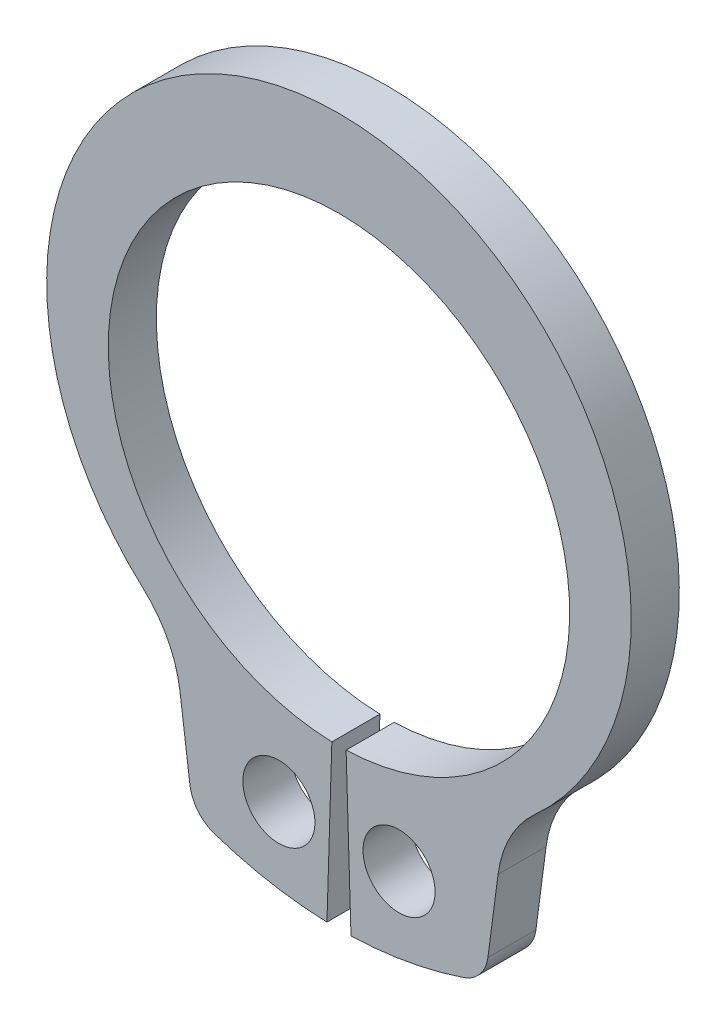
SolidWorks part; units mm, degrees
ref_plane "Plane1" through (0, 0, 0) normal (0, 0, 1) x (1, 0, 0)
ref_plane "Plane2" through (0, 0, 0) normal (0, 1, 0) x (1, 0, 0)
ref_plane "Plane3" through (0, 0, 0) normal (1, 0, 0) x (0, 0, -1)
sketch "Clipboard" plane through (0, 0, 0) normal (0, 0, 1) x (1, 0, 0)
  line L0 (0, 0) -> (1.8, 0)
  line L1 (0, 0) -> (0, 0.9)
  line L2 (0, 0) -> (0, -3.3)
  circle A0 centre (0, 0) radius 0.75
  circle A1 centre (0, 0) radius 5
  dimension "HoleDia" = 1.5
  dimension "ShaftDia" = 10
  dimension "LargeSection" = 1.8
  dimension "SmallSection" = 0.9
  dimension "LugSection" = 3.3
sketch "BodySke" plane through (0, 0, 0) normal (0, 0, 1) x (1, 0, 0)
  line L0 (-1.5431, 0) -> (1.5431, 0) construction
  line L1 (0, 0) -> (0, 6.6) construction
  line L2 (0.1481, -4.7977) -> (0.25, -8.0961)
  line L3 (-0.1481, -4.7977) -> (-0.25, -8.0961)
  line L4 (0, 0) -> (5.6861, -5.7688) construction
  line L5 (0, 0) -> (-5.6861, -5.7688) construction
  line L7 (3.3097, -5.4559) -> (3.0984, -7.0605)
  line L8 (-3.3097, -5.4559) -> (-3.0984, -7.0605)
  circle A0 centre (0, 0) radius 4.8 construction
  arc A1 (0.1481, -4.7977) -> (-0.1481, -4.7977) centre (0, 0) ccw
  arc A2 (4.0013, -4.0595) -> (-4.0013, -4.0595) centre (0, 0.5193) ccw construction
  arc A3 (0.25, -8.0961) -> (2.5951, -7.673) centre (0, 0) ccw
  arc A4 (4.0784, -3.991) -> (3.3097, -5.4559) centre (5.6861, -5.7688) ccw
  arc A5 (-3.3097, -5.4559) -> (-4.0784, -3.991) centre (-5.6861, -5.7688) ccw
  arc A6 (-2.5951, -7.673) -> (-0.25, -8.0961) centre (0, 0) ccw
  arc A7 (4.0784, -3.991) -> (-4.0784, -3.991) centre (0, 0.5193) ccw
  arc A8 (-3.2816, -5.6686) -> (3.2816, -5.6686) centre (0, 0) ccw construction
  circle A9 centre (1.25, -6.4296) radius 0.75
  circle A10 centre (-1.25, -6.4296) radius 0.75
  arc A11 (3.0984, -7.0605) -> (2.5951, -7.673) centre (2.3548, -6.9626) cw
  arc A12 (-3.0984, -7.0605) -> (-2.5951, -7.673) centre (-2.3548, -6.9626) ccw
  point P28 (3.0395, -7.5081)
  point P31 (-3.0395, -7.5081)
  dimension "GrooveDia" = 9.6
  dimension "D3" = 0.75
  dimension "LugRad" = 8.1
  dimension "HoleOffsetRad" = 6.55
  dimension "HoleDia" = 1.5
  dimension "D2" = 15
  dimension "LargeRad" = 6.6
  dimension "SmallRad" = 5.7
  dimension "Gap" = 0.5
  dimension "SmallAngle" = 89.172
  dimension "HoleSpacing" = 2.5
extrude "Body" add sketch "BodySke" against normal blind 1
sketch "NotSke" plane through (0, 0, 0) normal (0, 0, 1) x (1, 0, 0)
  line L0 (1.25, -5.6796) -> (1.25, -7.1796)
  line L1 (1.25, -7.1796) -> (-1.25, -7.1796)
  line L2 (-1.25, -7.1796) -> (-1.25, -5.6796)
  line L3 (-1.25, -5.6796) -> (1.25, -5.6796)
  circle A0 centre (1.25, -6.4296) radius 0.75 construction
  circle A1 centre (-1.25, -6.4296) radius 0.75 construction
extrude "Notch" [suppressed] cut sketch "NotSke" against normal through all
sketch "UnlSke" plane through (0, 0, 0) normal (0, 0, 1) x (1, 0, 0)
  line L0 (-2.4461, -7.7218) -> (-1.4495, -4.5759)
  line L1 (2.4461, -7.7218) -> (1.4495, -4.5759)
  arc A0 (1.4495, -4.5759) -> (-1.4495, -4.5759) centre (0, 0) ccw
  arc A1 (2.4461, -7.7218) -> (-2.4461, -7.7218) centre (0, 0) ccw
  arc A2 (0.25, -8.0961) -> (2.5951, -7.673) centre (0, 0) ccw construction
  arc A3 (0.1481, -4.7977) -> (-0.1481, -4.7977) centre (0, 0) ccw construction
  circle A4 centre (-1.25, -6.4296) radius 0.75 construction
  circle A5 centre (1.25, -6.4296) radius 0.75 construction
extrude "Unlug" [suppressed] add sketch "UnlSke" against normal through all
equation "' \"ShaftDia@Clipboard\" = 3"
equation "' \"Thickness@Body\" = 0.4"
equation "' \"GrooveDia@BodySke\" = 2.8"
equation "' \"LugSection@Clipboard\" = 1.9"
equation "' \"LargeSection@Clipboard\" = 0.8"
equation "' \"HoleDia@Clipboard\" = 1.0"
equation "' \"ShaftDia@Clipboard\" = 10"
equation "' \"Thickness@Body\" = 1.0"
equation "' \"GrooveDia@BodySke\" = 9.6"
equation "' \"LugSection@Clipboard\" = 3.3"
equation "' \"LargeSection@Clipboard\" = 1.8"
equation "' \"HoleDia@Clipboard\" = 1.5"
equation "\"SmallSection@Clipboard\" = \"LargeSection@Clipboard\" * 0.5"
equation "\"Gap@BodySke\" =  \"Thickness@Body\" / 2"
equation "\"LargeRad@BodySke\" =  \"GrooveDia@BodySke\" / 2 +  \"LargeSection@Clipboard\""
equation "\"SmallRad@BodySke\" =  \"GrooveDia@BodySke\" / 2 +  \"SmallSection@Clipboard\""
equation "\"LugRad@BodySke\" = \"GrooveDia@BodySke\" / 2 + \"LugSection@Clipboard\""
equation "\"HoleOffsetRad@BodySke\" = (  \"ShaftDia@Clipboard\" / 2 + \"LugRad@BodySke\" ) / 2"
equation "\"HoleSpacing@BodySke\" = \"Gap@BodySke\"  * 2 +  \"HoleDia@Clipboard\""
equation "\"HoleDia@BodySke\" =  \"HoleDia@Clipboard\""
equation "\"SmallAngle@BodySke\" = atn(\"HoleSpacing@BodySke\" / 2 / sqr(\"HoleOffsetRad@BodySke\"  * \"HoleOffsetRad@BodySke\" - (\"HoleSpacing@BodySke\" / 2) * (\"HoleSpacing@BodySke\" / 2) ))  * 7 *  (\"LargeRad@BodySke\" / \"SmallRad@BodySke\")* ( 180 / 3.141593)"
